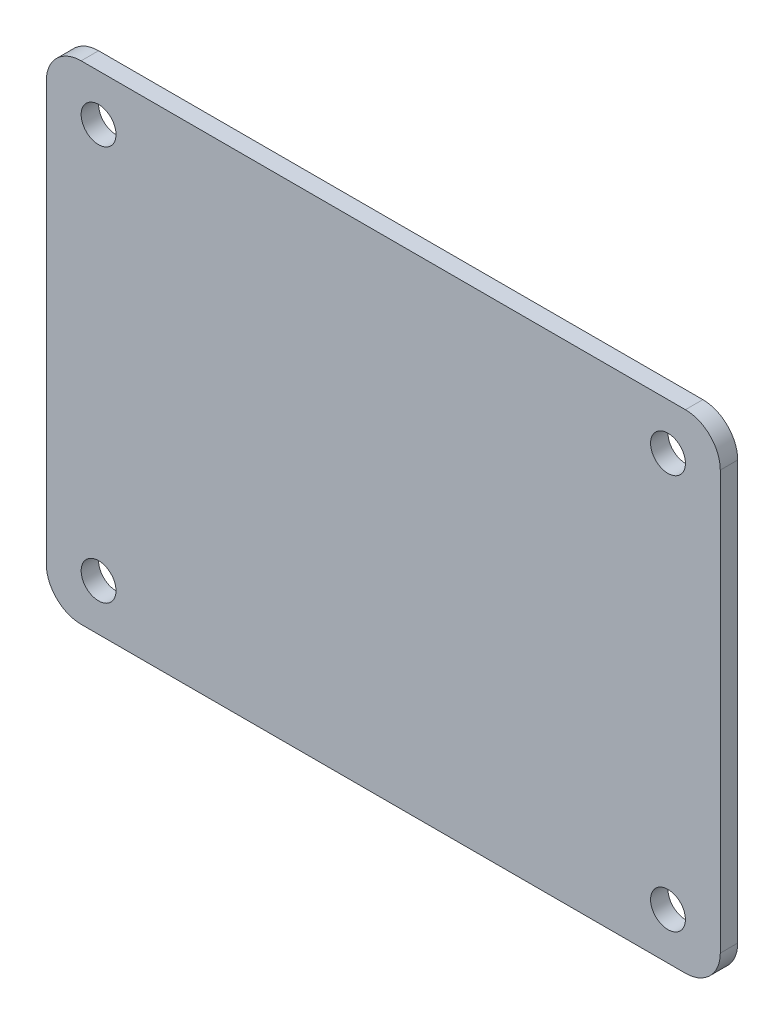
SolidWorks part; units mm, degrees
ref_plane "前视基准面" through (0, 0, 0) normal (0, 0, 1) x (1, 0, 0)
ref_plane "上视基准面" through (0, 0, 0) normal (0, 1, 0) x (1, 0, 0)
ref_plane "右视基准面" through (0, 0, 0) normal (1, 0, 0) x (0, 0, -1)
sketch "草图1" plane through (0, 0, 0) normal (0, 0, 1) x (1, 0, 0)
  line L1 (-29, 21) -> (29, 21)
  line L2 (-29, 21) -> (-29, -21)
  line L3 (-29, -21) -> (29, -21)
  line L4 (29, 21) -> (29, -21)
  line L5 (-29, 21) -> (29, -21) construction
  line L6 (-29, -21) -> (29, 21) construction
  point P0 (0, 0)
  dimension "D1" = 58
  dimension "D2" = 42
extrude "凸台-拉伸1" add sketch "草图1" along normal blind 1.5
sketch "草图2" plane through (0, 0, 1.5) normal (0, 0, 1) x (1, 0, 0)
  line L1 (-24.5, 17) -> (24.5, 17) construction
  line L2 (-24.5, 17) -> (-24.5, -17) construction
  line L3 (-24.5, -17) -> (24.5, -17) construction
  line L4 (24.5, 17) -> (24.5, -17) construction
  line L5 (-24.5, 17) -> (24.5, -17) construction
  line L6 (-24.5, -17) -> (24.5, 17) construction
  circle A0 centre (-24.5, 17) radius 1.5
  circle A1 centre (-24.5, -17) radius 1.5
  circle A2 centre (24.5, -17) radius 1.5
  circle A3 centre (24.5, 17) radius 1.5
  point P0 (0, 0)
  dimension "D3" = 3
  dimension "D1" = 49
  dimension "D2" = 34
extrude "切除-拉伸1" cut sketch "草图2" against normal blind 1.5
fillet "圆角1" radius 3 4 edges at (29, 21, 0.75) (29, -21, 0.75) (-29, -21, 0.75) (-29, 21, 0.75)
